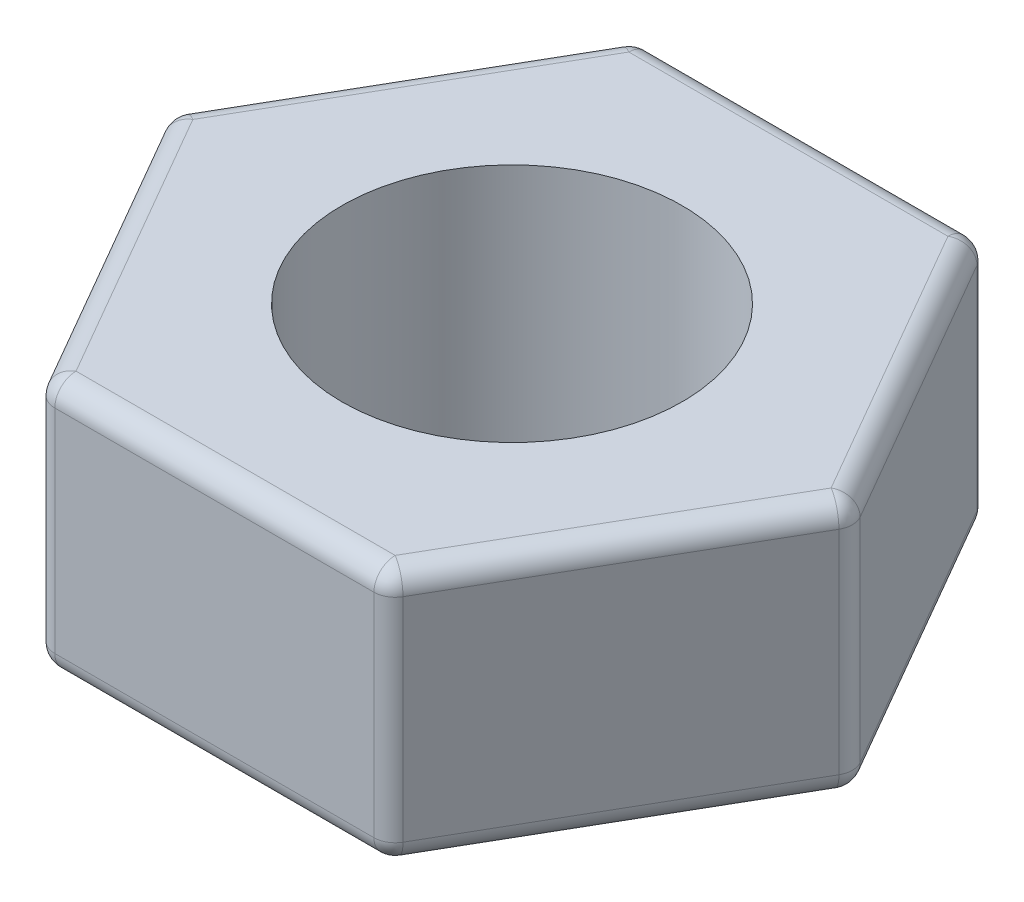
SolidWorks part; units mm, degrees
material "Galvanized Steel"
ref_plane "Front Plane" through (0, 0, 0) normal (0, 0, 1) x (1, 0, 0)
ref_plane "Top Plane" through (0, 0, 0) normal (0, 1, 0) x (1, 0, 0)
ref_plane "Right Plane" through (0, 0, 0) normal (1, 0, 0) x (0, 0, -1)
sketch "Sketch1" plane through (0, 0, 0) normal (0, 1, 0) x (1, 0, 0)
  line L1 (-2.0207, 3.5) -> (-4.0415, 0)
  line L2 (-4.0415, 0) -> (-2.0207, -3.5)
  line L3 (-2.0207, -3.5) -> (2.0207, -3.5)
  line L4 (2.0207, -3.5) -> (4.0415, 0)
  line L5 (4.0415, 0) -> (2.0207, 3.5)
  line L6 (2.0207, 3.5) -> (-2.0207, 3.5)
  circle A0 centre (0, 0) radius 3.5 construction
  circle A1 centre (0, 0) radius 2
  dimension "D2" = 4
  dimension "D1" = 7
extrude "Boss-Extrude1" add sketch "Sketch1" along normal blind 3
fillet "Fillet1" radius 0.25 18 edges at (0, 0, -3.5) (2.0207, 1.5, -3.5) (3.0311, 0, -1.75) (-3.0311, 0, -1.75) (-2.0207, 1.5, -3.5) (0, 3, -3.5) (3.0311, 3, -1.75) (4.0415, 1.5, 0) (3.0311, 0, 1.75) (0, 0, 3.5) (-3.0311, 0, 1.75) (-4.0415, 1.5, 0) (-3.0311, 3, -1.75) (3.0311, 3, 1.75) (2.0207, 1.5, 3.5) (-2.0207, 1.5, 3.5) (-3.0311, 3, 1.75) (0, 3, 3.5)
